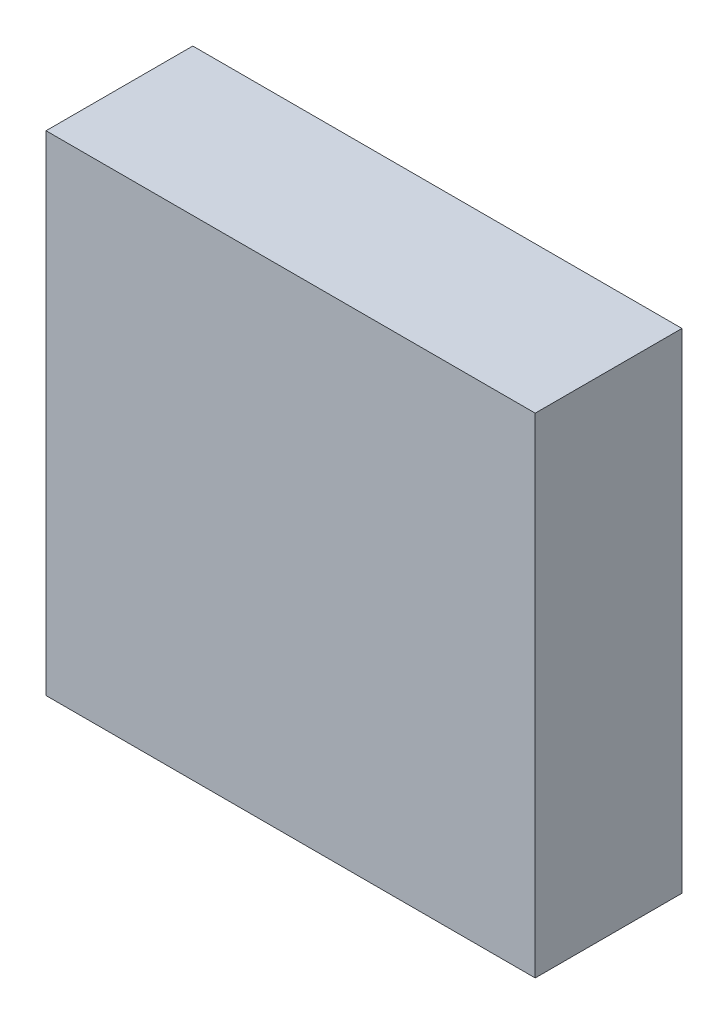
SolidWorks part; units mm, degrees
ref_plane "Front Plane" through (0, 0, 0) normal (1, 0, 0) x (0, 1, 0)
ref_plane "Top Plane" through (0, 0, 0) normal (0, 0, 1) x (0, 1, 0)
ref_plane "Right Plane" through (0, 0, 0) normal (0, 1, 0) x (-1, 0, 0)
sketch "Sketch1" plane through (0, 0, 0) normal (0, 0, 1) x (0, 1, 0)
  line L1 (0, 0) -> (32, 0)
  line L2 (0, 0) -> (0, 32)
  line L3 (0, 32) -> (32, 32)
  line L4 (32, 0) -> (32, 32)
  dimension "D1" = 32
  dimension "D2" = 32
extrude "Boss-Extrude1" add sketch "Sketch1" along normal blind 9.6
